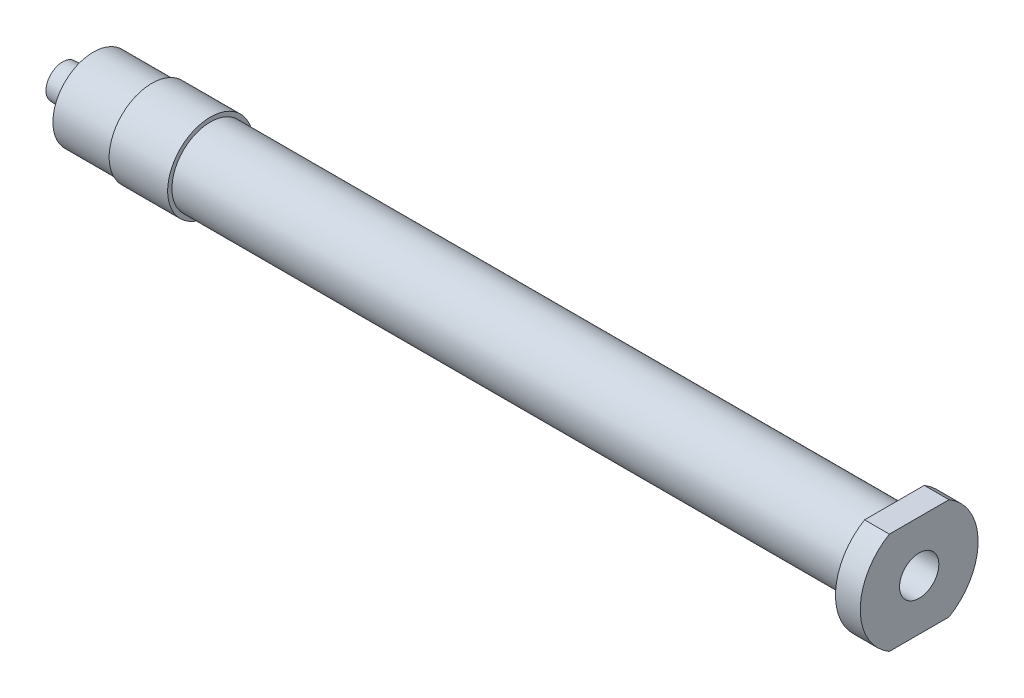
SolidWorks part; units mm, degrees
material "Silicon"
ref_plane "Front Plane" through (0, 0, 0) normal (0, 0, 1) x (1, 0, 0)
ref_plane "Top Plane" through (0, 0, 0) normal (0, 1, 0) x (1, 0, 0)
ref_plane "Right Plane" through (0, 0, 0) normal (1, 0, 0) x (0, 0, -1)
sketch "Sketch1" plane through (0, 0, 0) normal (0, 1, 0) x (1, 0, 0)
  line L0 (131.3608, 156.595) -> (606.2677, -140.1598) construction
  line L1 (-50.15, 4.5) -> (50.15, 4.5) construction
  line L2 (-50.15, 4.5) -> (-50.15, -4.5) construction
  line L3 (-50.15, -4.5) -> (50.15, -4.5) construction
  line L4 (50.15, 4.5) -> (50.15, -4.5) construction
  line L5 (-50.15, 4.5) -> (50.15, -4.5) construction
  line L6 (-50.15, -4.5) -> (50.15, 4.5) construction
  line L7 (50.15, 0) -> (-50.15, 0) construction
  line L8 (-39.7, 5) -> (-39.7, -5) construction
  line L9 (-46.55, 5) -> (-32.85, 5) construction
  line L10 (-46.55, 5) -> (-46.55, -5) construction
  line L11 (-46.55, -5) -> (-32.85, -5) construction
  line L12 (-32.85, 5) -> (-32.85, -5) construction
  line L13 (47.25, 6.9) -> (50.15, 6.9) construction
  line L14 (47.25, 6.9) -> (47.25, -6.9) construction
  line L15 (47.25, -6.9) -> (50.15, -6.9) construction
  line L16 (50.15, 6.9) -> (50.15, -6.9) construction
  line L17 (-46.55, 0) -> (-32.85, 0) construction
  line L18 (47.25, 0) -> (50.15, 0) construction
  line L19 (-46.55, 4.74) -> (-32.85, 4.74) construction
  line L20 (-50.15, 1.95) -> (-61.5766, 1.95) construction
  line L21 (-50.15, 1.95) -> (-43.05, 2.3221) construction
  line L22 (50.15, 2.3) -> (-50.15, 2.3) construction
  line L23 (-50.15, 0.75) -> (-32.85, 0.75) construction
  line L24 (-50.15, 0.75) -> (-50.15, 1.95)
  line L25 (-50.15, 1.95) -> (-43.05, 2.3221)
  line L26 (-43.05, 2.3221) -> (-43.05, 4.1)
  line L27 (-43.05, 4.1) -> (-46.55, 4.1)
  line L28 (-46.55, 4.1) -> (-46.55, 4.74)
  line L29 (-46.55, 4.74) -> (-39.7, 4.74)
  line L30 (-39.7, 4.74) -> (-39.7, 5)
  line L31 (-39.7, 5) -> (-32.85, 5)
  line L32 (-32.85, 5) -> (-32.85, 4.5)
  line L33 (-32.85, 4.5) -> (47.25, 4.5)
  line L34 (-50.15, 0.75) -> (-32.85, 0.75)
  line L35 (-32.85, 0.75) -> (-32.85, 2.3)
  line L36 (-32.85, 2.3) -> (50.15, 2.3)
  line L37 (47.25, 4.5) -> (47.25, 6.9)
  line L38 (47.25, 6.9) -> (50.15, 6.9)
  line L39 (50.15, 6.9) -> (50.15, 2.3)
  point P0 (0, 0)
  dimension "D1" = 100.3
  dimension "D2" = 9
  dimension "D3" = 10
  dimension "D4" = 13.7
  dimension "D5" = 0.26
  dimension "D6" = 3.6
  dimension "D7" = 1.95
  dimension "D8" = 3
  dimension "D10" = 0.75
  dimension "D11" = 0.9
  dimension "D12" = 3.5
  dimension "D13" = 2.9
  dimension "D14" = 13.8
  dimension "D9" = 2.3
revolve "Revolve1" add sketch "Sketch1" angle 360 about L7
sketch "Sketch2" plane through (50.15, 0, 0) normal (1, 0, 0) x (0, 0, -1)
  line L0 (-9.5, -7.95) -> (9.5, -7.95)
  line L1 (-7.5, 5.95) -> (7.5, 5.95)
  line L2 (-7.5, 5.95) -> (-7.5, -5.95)
  line L3 (-7.5, -5.95) -> (7.5, -5.95)
  line L4 (7.5, 5.95) -> (7.5, -5.95)
  line L5 (-7.5, 5.95) -> (7.5, -5.95) construction
  line L6 (-7.5, -5.95) -> (7.5, 5.95) construction
  line L7 (9.5, 7.95) -> (9.5, -7.95)
  line L8 (-9.5, 7.95) -> (9.5, 7.95)
  line L9 (-9.5, 7.95) -> (-9.5, -7.95)
  point P0 (0, 0)
  dimension "D1" = 11.9
  dimension "D2" = 2
  dimension "D3" = 15
extrude "Cut-Extrude1" cut sketch "Sketch2" against normal up to surface (2.9 mm away) up to face at (47.25, 0, -4.5)
